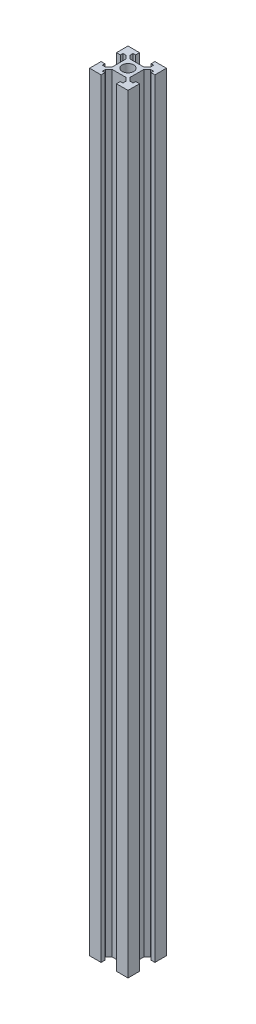
SolidWorks part; units mm, degrees
ref_plane "Front Plane" through (0, 0, 0) normal (0, 0, 1) x (1, 0, 0)
ref_plane "Top Plane" through (0, 0, 0) normal (0, 1, 0) x (1, 0, 0)
ref_plane "Right Plane" through (0, 0, 0) normal (1, 0, 0) x (0, 0, -1)
sketch "Sketch1" plane through (0, 0, 0) normal (0, 1, 0) x (1, 0, 0)
  line L0 (-30, 0) -> (30, 0) construction
  line L3 (-30, 30) -> (-12, 30)
  line L5 (-30, -30) -> (30, 30) construction
  line L6 (-30, 30) -> (30, -30) construction
  line L7 (0, 30) -> (0, -30) construction
  line L8 (-30, 12) -> (-24, 12)
  line L13 (-24, -24) -> (24, 24) construction
  line L14 (-24, 24) -> (24, -24) construction
  line L15 (-14, 24) -> (-14, 16) construction
  line L16 (-24, 16) -> (-19, 16)
  line L17 (-19, 16) -> (-14, 11)
  line L18 (-30, 12) -> (-30, 30)
  line L19 (-14, 11) -> (-14, -11)
  line L20 (-24, 12) -> (-24, 16)
  line L21 (-11, 14) -> (11, 14)
  line L22 (-16, 19) -> (-11, 14)
  line L23 (-12, 24) -> (-16, 24)
  line L24 (-16, 24) -> (-16, 19)
  line L25 (-12, 30) -> (-12, 24)
  line L26 (12, 30) -> (30, 30)
  line L27 (12, 30) -> (12, 24)
  line L28 (12, 24) -> (16, 24)
  line L29 (16, 24) -> (16, 19)
  line L30 (16, 19) -> (11, 14)
  line L31 (14, 11) -> (14, -11)
  line L32 (19, 16) -> (14, 11)
  line L33 (24, 12) -> (24, 16)
  line L34 (24, 16) -> (19, 16)
  line L35 (30, 12) -> (24, 12)
  line L36 (30, 12) -> (30, 30)
  line L37 (-14, -24) -> (-14, -16) construction
  line L38 (30, -12) -> (30, -30)
  line L39 (30, -12) -> (24, -12)
  line L40 (24, -16) -> (19, -16)
  line L41 (24, -12) -> (24, -16)
  line L42 (19, -16) -> (14, -11)
  line L43 (16, -19) -> (11, -14)
  line L44 (16, -24) -> (16, -19)
  line L45 (12, -24) -> (16, -24)
  line L46 (12, -30) -> (12, -24)
  line L47 (12, -30) -> (30, -30)
  line L48 (-12, -30) -> (-12, -24)
  line L49 (-16, -24) -> (-16, -19)
  line L50 (-12, -24) -> (-16, -24)
  line L51 (-16, -19) -> (-11, -14)
  line L52 (-11, -14) -> (11, -14)
  line L53 (-24, -12) -> (-24, -16)
  line L54 (-30, -12) -> (-30, -30)
  line L55 (-19, -16) -> (-14, -11)
  line L56 (-24, -16) -> (-19, -16)
  line L57 (-30, -12) -> (-24, -12)
  line L58 (-30, -30) -> (-12, -30)
  circle A0 centre (0, 0) radius 9
  point P0 (0, 0)
  point P10 (0, 0)
  point P34 (0, 14)
  point P41 (-14, 0)
  point P42 (14, 0)
  point P62 (0, -14)
  dimension "D1" = 18
  dimension "D3" = 12
  dimension "D5" = 16
  dimension "D6" = 5
  dimension "D7" = 5
  dimension "D8" = 6
extrude "Boss-Extrude1" add sketch "Sketch1" along normal blind 1200
